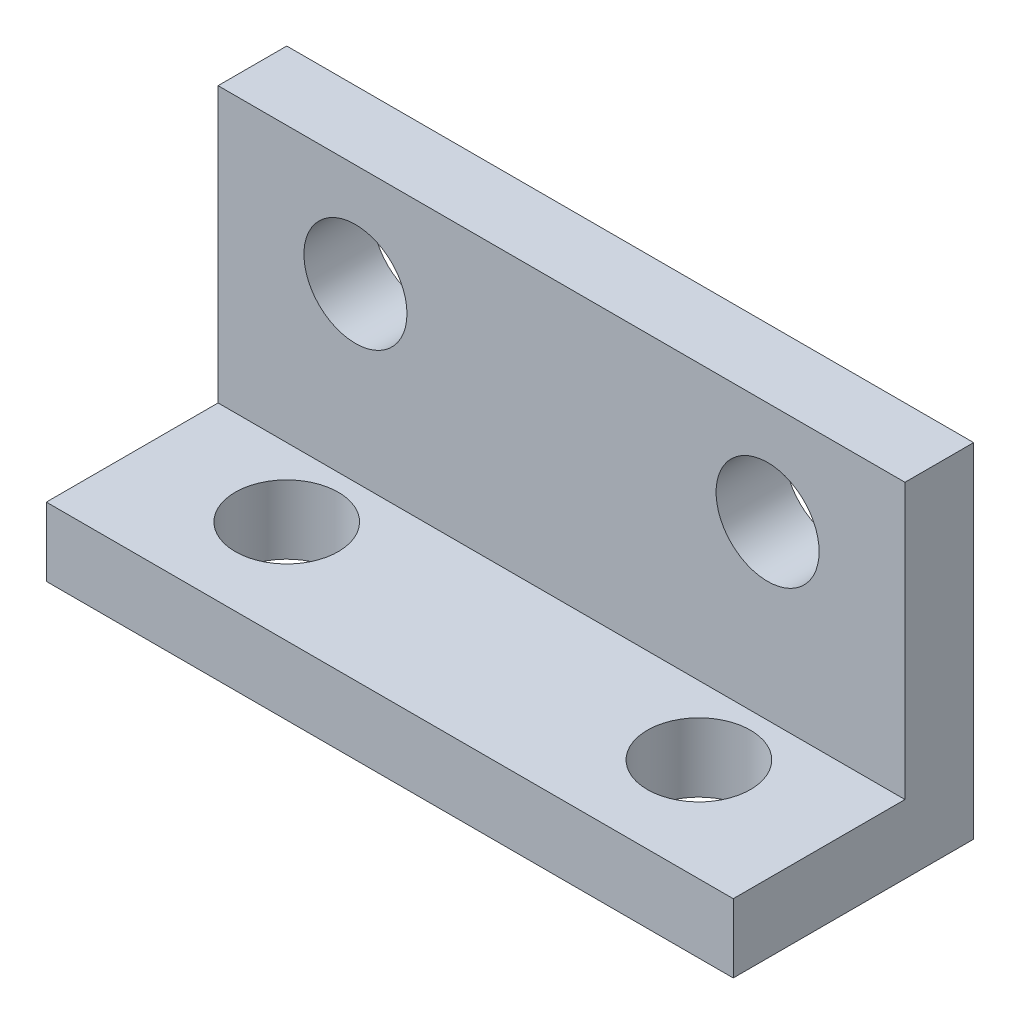
SolidWorks part; units mm, degrees
ref_plane "Plano frontal" through (0, 0, 0) normal (0, 0, 1) x (1, 0, 0)
ref_plane "Plano superior" through (0, 0, 0) normal (0, 1, 0) x (1, 0, 0)
ref_plane "Plano direito" through (0, 0, 0) normal (1, 0, 0) x (0, 0, -1)
sketch "Esboço1" plane through (0, 0, 0) normal (1, 0, 0) x (0, 0, -1)
  line L0 (0, 0) -> (0, 10)
  line L1 (0, 0) -> (-7, 0)
  line L2 (-2, 2) -> (-2, 10)
  line L3 (-2, 2) -> (-7, 2)
  line L4 (0, 10) -> (-2, 10)
  line L5 (-7, 0) -> (-7, 2)
  dimension "D2" = 7
  dimension "D3" = 10
  dimension "D1" = 2
extrude "Ressalto-extrusão1" add sketch "Esboço1" along normal blind 20
sketch "Esboço2" plane through (0, 2, 0) normal (0, 1, 0) x (1, 0, 0)
  line L0 (4, -4) -> (16, -4) construction
  line L1 (10, -4) -> (10, -7) construction
  line L2 (20, -7) -> (0, -7) construction
  circle A0 centre (4, -4) radius 1.5
  circle A1 centre (16, -4) radius 1.5
  dimension "D2" = 3
  dimension "D1" = 12
  dimension "D3" = 3
extrude "Corte-extrusão1" cut sketch "Esboço2" against normal through all
sketch "Esboço3" plane through (0, 0, 2) normal (0, 0, 1) x (1, 0, 0)
  line L0 (10, 2) -> (10, 7) construction
  line L1 (20, 2) -> (0, 2) construction
  line L2 (4, 7) -> (16, 7) construction
  circle A0 centre (4, 7) radius 1.5
  circle A1 centre (16, 7) radius 1.5
  point P8 (10, 7)
  dimension "D1" = 3
  dimension "D2" = 12
  dimension "D3" = 5
extrude "Corte-extrusão2" cut sketch "Esboço3" against normal through all
